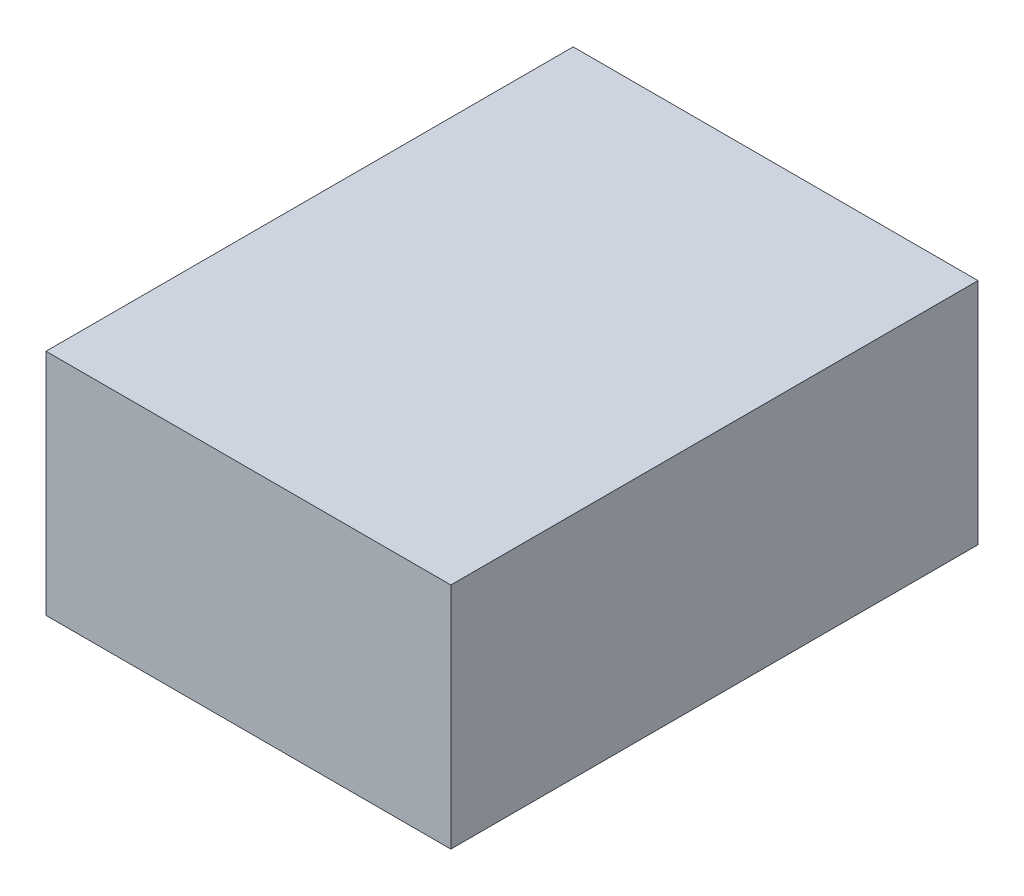
SolidWorks part; units mm, degrees
ref_plane "Ön Düzlem" through (0, 0, 0) normal (0, 0, 1) x (1, 0, 0)
ref_plane "Üst Düzlem" through (0, 0, 0) normal (0, 1, 0) x (1, 0, 0)
ref_plane "Sağ Düzlem" through (0, 0, 0) normal (1, 0, 0) x (0, 0, -1)
sketch "Çizim1" plane through (0, 0, 0) normal (0, 0, 1) x (1, 0, 0)
  line L1 (-51.689, 29.21) -> (51.689, 29.21)
  line L2 (-51.689, 29.21) -> (-51.689, -29.21)
  line L3 (-51.689, -29.21) -> (51.689, -29.21)
  line L4 (51.689, 29.21) -> (51.689, -29.21)
  line L5 (-51.689, 29.21) -> (51.689, -29.21) construction
  line L6 (-51.689, -29.21) -> (51.689, 29.21) construction
  point P0 (0, 0)
  dimension "D1" = 103.378
  dimension "D2" = 58.42
extrude "Yükseklik-Ekstrüzyon1" add sketch "Çizim1" along normal blind 67.31 and the other way blind 67.31
